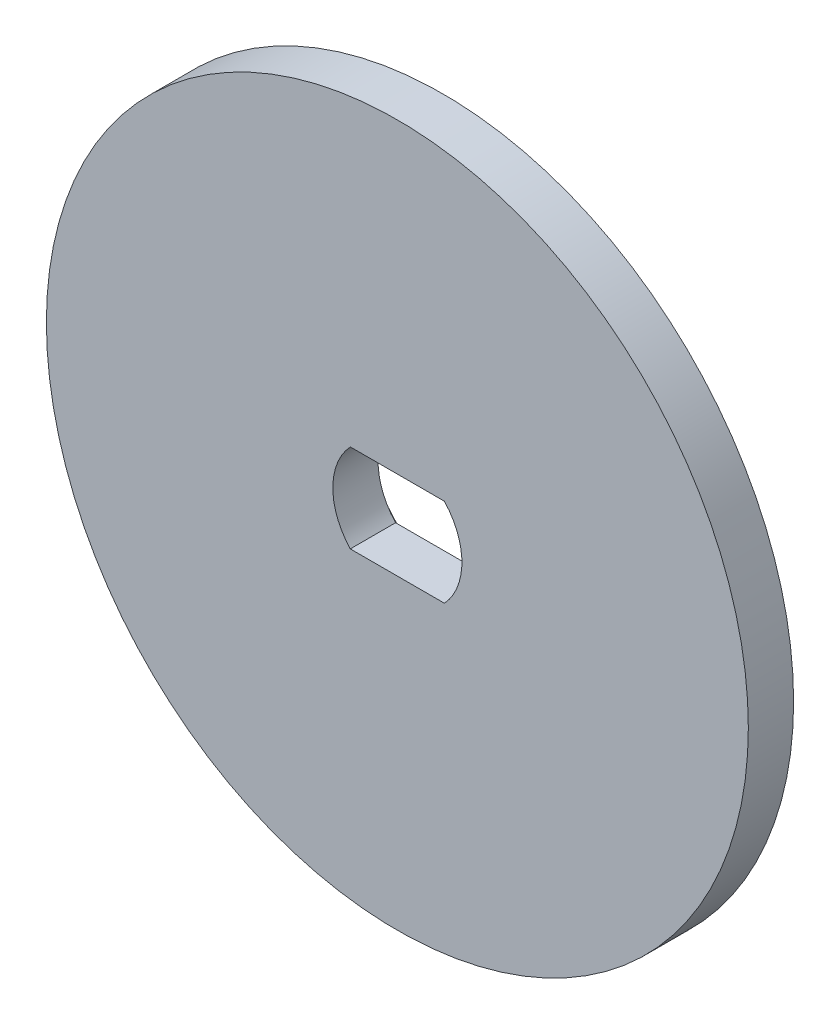
SolidWorks part; units mm, degrees
ref_plane "Front Plane" through (0, 0, 0) normal (0, 0, 1) x (1, 0, 0)
ref_plane "Top Plane" through (0, 0, 0) normal (0, 1, 0) x (1, 0, 0)
ref_plane "Right Plane" through (0, 0, 0) normal (1, 0, 0) x (0, 0, -1)
sketch "Sketch1" plane through (0, 0, 0) normal (0, 0, 1) x (1, 0, 0)
  circle A0 centre (0, 0) radius 15.5 construction
  circle A1 centre (0, 0) radius 15.5
extrude "Boss-Extrude1" add sketch "Sketch1" along normal blind 2
sketch "Sketch2" plane through (0, 0, 0) normal (0, 0, -1) x (-1, 0, 0)
  line L0 (-7.8174, 8.129) -> (-3.5527, 4.927)
  line L1 (0.2749, 6.0681) -> (2.0901, 11.0826)
  line L2 (-7.8774, 8.0491) -> (-3.6127, 4.8471)
  line L3 (0.3689, 6.0341) -> (2.1842, 11.0485)
  line L4 (-7.8774, 8.0491) -> (-3.6127, 4.8471) construction
  line L5 (0.3689, 6.0341) -> (2.1842, 11.0485) construction
  arc A0 (1.3416, 12.2836) -> (-7.8486, 9.5439) centre (0, 0) ccw
  arc A1 (-7.8486, 9.5439) -> (-7.8174, 8.129) centre (-7.277, 8.8488) ccw
  arc A2 (-3.5527, 4.927) -> (-2.5887, 4.8527) centre (-3.0123, 5.6468) ccw
  arc A3 (-0.491, 5.478) -> (-2.5887, 4.8527) centre (0, 0) ccw
  arc A4 (-0.491, 5.478) -> (0.2749, 6.0681) centre (-0.5714, 6.3744) ccw
  arc A5 (2.0901, 11.0826) -> (1.3416, 12.2836) centre (1.2439, 11.3889) ccw
  arc A6 (1.3524, 12.383) -> (-7.9122, 9.6211) centre (0, 0) ccw
  arc A7 (-7.9122, 9.6211) -> (-7.8774, 8.0491) centre (-7.277, 8.8488) ccw
  arc A8 (-3.6127, 4.8471) -> (-2.5416, 4.7645) centre (-3.0123, 5.6468) ccw
  arc A9 (-0.4821, 5.3784) -> (-2.5416, 4.7645) centre (0, 0) ccw
  arc A10 (-0.4821, 5.3784) -> (0.3689, 6.0341) centre (-0.5714, 6.3744) ccw
  arc A11 (2.1842, 11.0485) -> (1.3524, 12.383) centre (1.2439, 11.3889) ccw
  arc A12 (1.3524, 12.383) -> (-7.9122, 9.6211) centre (0, 0) ccw construction
  arc A13 (-7.9122, 9.6211) -> (-7.8774, 8.0491) centre (-7.277, 8.8488) ccw construction
  arc A14 (-3.6127, 4.8471) -> (-2.5416, 4.7645) centre (-3.0123, 5.6468) ccw construction
  arc A15 (-0.4821, 5.3784) -> (-2.5416, 4.7645) centre (0, 0) ccw construction
  arc A16 (-0.4821, 5.3784) -> (0.3689, 6.0341) centre (-0.5714, 6.3744) ccw construction
  arc A17 (2.1842, 11.0485) -> (1.3524, 12.383) centre (1.2439, 11.3889) ccw construction
  dimension "D1" = 0
  dimension "D2" = 0.1
extrude "Boss-Extrude2" add sketch "Sketch2" along normal offset from surface (1.9 mm away) 0.3
pattern_circular "CirPattern1" count 5 over 360 about axis through (0, 0, 0) along (0, 0, 1) of "Boss-Extrude2"
sketch "Sketch5" plane through (0, 0, 2) normal (0, 0, 1) x (1, 0, 0)
  line L0 (-2.0785, 1.95) -> (2.0785, 1.95)
  line L1 (2.0785, -1.95) -> (-2.0785, -1.95)
  arc A0 (-2.0785, 1.95) -> (-2.0785, -1.95) centre (0, 0) ccw
  arc A1 (2.0785, -1.95) -> (2.0785, 1.95) centre (0, 0) ccw
  dimension "D1" = 5.7
  dimension "D2" = 3.9
extrude "Cut-Extrude2" cut sketch "Sketch5" against normal through all
